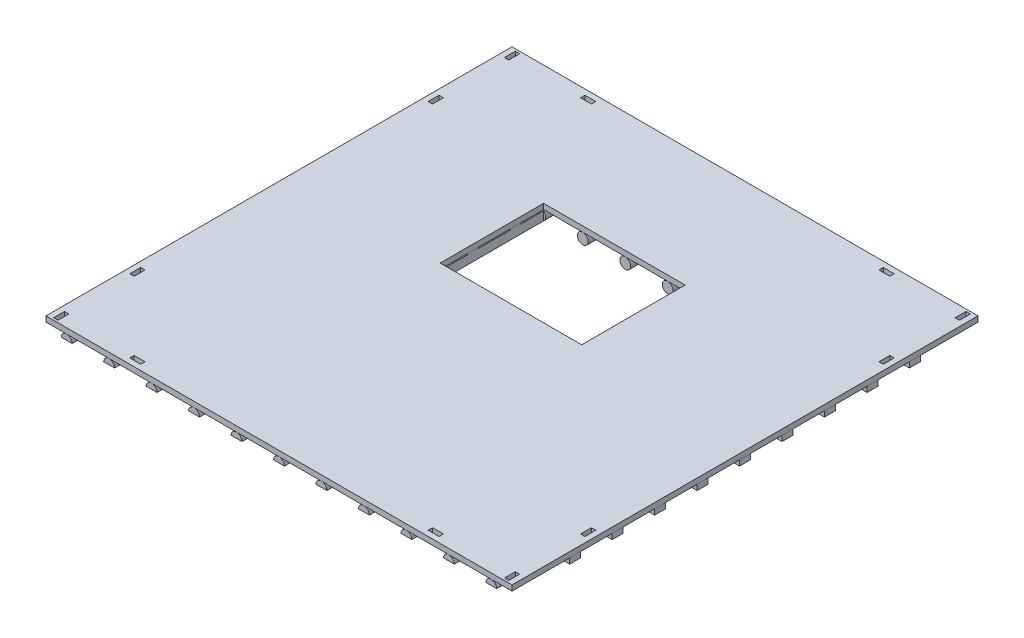
SolidWorks part; units mm, degrees
material "松木"
ref_plane "前视基准面" through (0, 0, 0) normal (0, 0, 1) x (1, 0, 0)
ref_plane "上视基准面" through (0, 0, 0) normal (0, 1, 0) x (1, 0, 0)
ref_plane "右视基准面" through (0, 0, 0) normal (1, 0, 0) x (0, 0, -1)
sketch "草图1" plane through (0, 0, 0) normal (0, 1, 0) x (1, 0, 0)
  line L1 (0, 0) -> (4280, 0)
  line L2 (0, 0) -> (0, 4280)
  line L3 (0, 4280) -> (4280, 4280)
  line L4 (4280, 0) -> (4280, 4280)
  dimension "D1" = 4280
  dimension "D2" = 4280
extrude "凸台-拉伸1" add sketch "草图1" along normal blind 50 contours L2 L1 L4 L3
sketch "草图2" plane through (0, 0, 0) normal (0, 0, 1) x (1, 0, 0)
  line L0 (0, 0) -> (140, 0)
  line L1 (0, 0) -> (4280, 0) construction
  circle A0 centre (190, -50) radius 50
  dimension "D2" = 100
  dimension "D1" = 140
  dimension "D3" = 50
extrude "凸台-拉伸3" add sketch "草图2" against normal blind 4280 separate body contours A0
sketch "草图3" plane through (0, 0, 0) normal (0, 0, 1) x (1, 0, 0)
  line L0 (0, 0) -> (4280, 0) construction
  line L1 (140, -50) -> (240, -50)
  line L2 (140, -50) -> (140, -150)
  line L3 (140, -150) -> (240, -150)
  line L4 (240, -50) -> (240, -150)
  dimension "D1" = 100
  dimension "D2" = 100
  dimension "D3" = 140
  dimension "D4" = 50
extrude "切除-拉伸1" cut sketch "草图3" against normal blind 140
sketch "草图4" plane through (0, 0, -4280) normal (0, 0, -1) x (-1, 0, 0)
  line L0 (0, 0) -> (-4280, 0) construction
  line L1 (-240, -150) -> (-140, -150)
  line L2 (-240, -150) -> (-240, -50)
  line L3 (-240, -50) -> (-140, -50)
  line L4 (-140, -150) -> (-140, -50)
  dimension "D1" = 100
  dimension "D2" = 100
  dimension "D3" = 50
  dimension "D4" = 140
extrude "切除-拉伸2" cut sketch "草图4" against normal blind 140
pattern_linear "阵列(线性)2" count 11 spacing 390 along (1, 0, 0) of "凸台-拉伸3", "切除-拉伸1", "切除-拉伸2"
sketch "草图5" plane through (4280, 0, 0) normal (1, 0, 0) x (0, 0, -1)
  line L0 (0, 0) -> (4280, 0) construction
  line L1 (530, 0) -> (630, 0)
  line L2 (530, 0) -> (530, -30)
  line L3 (530, -30) -> (630, -30)
  line L4 (630, 0) -> (630, -30)
  dimension "D1" = 530
  dimension "D2" = 30
  dimension "D3" = 100
extrude "切除-拉伸3" cut sketch "草图5" against normal blind 4280
sketch "草图6" plane through (4280, 0, 0) normal (1, 0, 0) x (0, 0, -1)
  line L1 (630, -30) -> (530, -30)
  line L2 (630, -30) -> (630, -0.01)
  line L3 (630, -0.01) -> (530, -0.01)
  line L4 (530, -30) -> (530, -0.01)
  line L7 (0, 50) -> (4280, 50) construction
  dimension "D1" = 100
  dimension "D2" = 29.99
  dimension "D3" = 530
  dimension "D4" = 50.01
extrude "凸台-拉伸6" add sketch "草图6" against normal blind 4280
sketch "草图7" plane through (0, -30, 0) normal (0, -1, 0) x (1, 0, 0)
  line L0 (4135.8258, -530) -> (4280, -530) construction
  line L1 (4280, -630) -> (4180, -630)
  line L2 (4280, -630) -> (4280, -530)
  line L3 (4280, -530) -> (4180, -530)
  line L4 (4180, -630) -> (4180, -530)
  dimension "D1" = 100
extrude "凸台-拉伸9" add sketch "草图7" along normal blind 20 contours L2 L1 L4 L3
sketch "草图8" plane through (0, -30, 0) normal (0, -1, 0) x (1, 0, 0)
  line L0 (0, -530) -> (144.1742, -530) construction
  line L1 (0, -630) -> (100, -630)
  line L2 (0, -630) -> (0, -530)
  line L3 (0, -530) -> (100, -530)
  line L4 (100, -630) -> (100, -530)
  dimension "D1" = 100
extrude "凸台-拉伸10" add sketch "草图8" along normal blind 20
pattern_linear "阵列(线性)3" count 9 spacing 390 along (0, 0, -1) of "凸台-拉伸10", "凸台-拉伸9", "凸台-拉伸6"
sketch "草图9" plane through (0, 0, 0) normal (0, -1, 0) x (1, 0, 0)
  line L0 (0, 0) -> (0, -4280) construction
  line L1 (50, -120) -> (90, -120)
  line L2 (50, -120) -> (50, -20)
  line L3 (50, -20) -> (90, -20)
  line L4 (90, -120) -> (90, -20)
  line L5 (0, 0) -> (4280, 0) construction
  dimension "D1" = 100
  dimension "D2" = 40
  dimension "D3" = 50
  dimension "D4" = 20
extrude "切除-拉伸4" cut sketch "草图9" against normal through all
pattern_linear "阵列(线性)4" count 2 spacing 4140 along (1, 0, 0) count 2 spacing 4140 along (0, 0, -1) of "切除-拉伸4"
sketch "草图10" plane through (0, 0, 0) normal (0, -1, 0) x (1, 0, 0)
  line L0 (0, 0) -> (0, -4280) construction
  line L1 (50, -720) -> (90, -720)
  line L2 (50, -720) -> (50, -820)
  line L3 (50, -820) -> (90, -820)
  line L4 (90, -720) -> (90, -820)
  line L5 (0, 0) -> (4280, 0) construction
  dimension "D1" = 100
  dimension "D2" = 40
  dimension "D3" = 50
  dimension "D4" = 720
extrude "切除-拉伸5" cut sketch "草图10" against normal through all
pattern_linear "阵列(线性)5" count 2 spacing 4140 along (1, 0, 0) of "切除-拉伸5"
pattern_linear "阵列(线性)6" count 2 spacing 2740 along (0, 0, -1) of "阵列(线性)5"
sketch "草图11" plane through (0, 0, 0) normal (0, -1, 0) x (1, 0, 0)
  line L0 (0, 0) -> (4280, 0) construction
  line L1 (820, -90) -> (720, -90)
  line L2 (820, -90) -> (820, -50)
  line L3 (820, -50) -> (720, -50)
  line L4 (720, -90) -> (720, -50)
  line L5 (0, 0) -> (0, -4280) construction
  dimension "D1" = 100
  dimension "D2" = 40
  dimension "D3" = 50
  dimension "D4" = 720
extrude "切除-拉伸6" cut sketch "草图11" against normal blind 100
pattern_linear "阵列(线性)7" count 2 spacing 2740 along (1, 0, 0) count 2 spacing 4140 along (0, 0, -1) of "切除-拉伸6"
sketch "草图12" plane through (0, 50, 0) normal (0, 1, 0) x (1, 0, 0)
  line L0 (0, 4280) -> (4280, 4280) construction
  line L1 (140, 4140) -> (1390, 4140)
  line L2 (140, 4140) -> (140, 2230)
  line L3 (140, 2230) -> (1390, 2230)
  line L4 (1390, 4140) -> (1390, 2230)
  line L6 (0, 0) -> (0, 4280) construction
  line L8 (1390, 2230) -> (440, 2230)
  line L9 (1390, 2230) -> (1390, 465)
  line L10 (1390, 465) -> (440, 465)
  line L11 (440, 2230) -> (440, 465)
  line L12 (1390, 2230) -> (2690, 2230)
  line L13 (1390, 2230) -> (1390, 3180)
  line L14 (1390, 3180) -> (2690, 3180)
  line L15 (2690, 2230) -> (2690, 3180)
  dimension "D1" = 1250
  dimension "D2" = 140
  dimension "D3" = 140
  dimension "D4" = 1910
  dimension "D5" = 1765
  dimension "D6" = 950
  dimension "D7" = 1300
  dimension "D8" = 950
extrude "切除-拉伸7" cut sketch "草图12" against normal through all contours L12 L15 L14 L4
